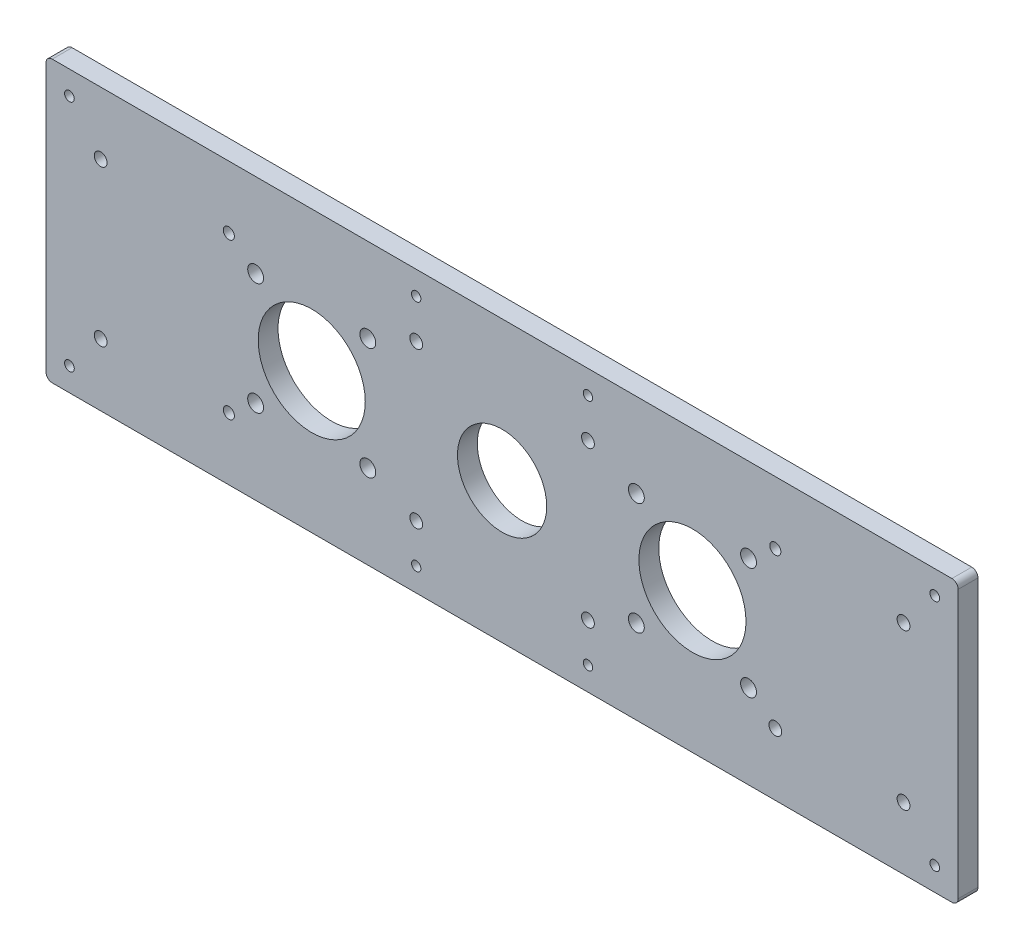
SolidWorks part; units mm, degrees
ref_plane "Front Plane" through (0, 0, 0) normal (0, 0, 1) x (1, 0, 0)
ref_plane "Top Plane" through (0, 0, 0) normal (0, 1, 0) x (1, 0, 0)
ref_plane "Right Plane" through (0, 0, 0) normal (1, 0, 0) x (0, 0, -1)
sketch "Sketch1" plane through (0, 0, 0) normal (0, 0, 1) x (1, 0, 0)
  line L1 (0, 0) -> (292.1, 0)
  line L2 (0, 0) -> (0, 89.8)
  line L3 (0, 89.8) -> (292.1, 89.8)
  line L4 (292.1, 0) -> (292.1, 89.8)
  circle A3 centre (146.05, 44.9) radius 14.2875
  point P7 (146.05, 44.9)
  circle B0 centre (103.0516, 62.8594) radius 2.54
  circle B1 centre (103.0494, 26.9384) radius 2.54
  circle B2 centre (67.1284, 26.9406) radius 2.54
  circle B3 centre (67.1306, 62.8616) radius 2.54
  circle B4 centre (85.09, 44.9) radius 17.145
  circle B5 centre (189.0506, 62.8616) radius 2.54
  circle B6 centre (224.9716, 62.8594) radius 2.54
  circle B7 centre (224.9694, 26.9384) radius 2.54
  circle B8 centre (189.0484, 26.9406) radius 2.54
  circle B9 centre (207.01, 44.9) radius 17.145
  dimension "D3" = 60.96
  dimension "D4" = 60.96
  dimension "D5" = 146.05
  dimension "D6" = 28.575
  dimension "D1" = 89.8
  dimension "D2" = 292.1
sketch_block_instance "Block1-1"
sketch_block "Block1" parameters "D1"=5.08, "D2"=34.29
sketch_block_instance "Block2-1"
sketch_block "Block2" parameters "D1"=5.08, "D2"=34.29
extrude "Boss-Extrude1" add sketch "Sketch1" along normal blind 6.35
sketch "Sketch2" plane through (0, 0, 6.35) normal (0, 0, 1) x (1, 0, 0)
  line L0 (292.1, 89.8) -> (0, 89.8) construction
  line L1 (108.55, 0) -> (183.55, 0)
  line L2 (108.55, 0) -> (108.55, 89.8)
  line L3 (108.55, 89.8) -> (183.55, 89.8)
  line L4 (183.55, 0) -> (183.55, 89.8)
  line L5 (108.55, 0) -> (183.55, 89.8) construction
  line L6 (108.55, 89.8) -> (183.55, 0) construction
  line L7 (108.55, 44.9) -> (146.05, 44.9) construction
  line L8 (108.55, 89.8) -> (-29.3949, 89.8)
  line L9 (108.55, 89.8) -> (108.55, -10.172)
  line L10 (108.55, -10.172) -> (-29.3949, -10.172)
  line L11 (-29.3949, 89.8) -> (-29.3949, -10.172)
  line L12 (183.55, 89.8) -> (343.3103, 89.8)
  line L13 (183.55, 89.8) -> (183.55, -29.3261)
  line L14 (183.55, -29.3261) -> (343.3103, -29.3261)
  line L15 (343.3103, 89.8) -> (343.3103, -29.3261)
  line L16 (146.05, 44.9) -> (146.05, 89.8) construction
  circle A0 centre (118.55, 20) radius 2.05
  circle A1 centre (118.55, 69.8) radius 2.05
  circle A2 centre (173.55, 20) radius 2.05
  circle A3 centre (173.55, 69.8) radius 2.05
  point P0 (146.05, 44.9)
  dimension "D2" = 4.1
  dimension "D3" = 20
  dimension "D1" = 75
  dimension "D4" = 10
extrude "Cut-Extrude1" cut sketch "Sketch2" against normal blind 10 contours A0 | A1 | A3 | A2
sketch "Sketch3" plane through (0, 0, 6.35) normal (0, 0, 1) x (1, 0, 0)
  line L0 (0, 0) -> (292.1, 0) construction
  line L1 (292.1, 0) -> (292.1, 89.8) construction
  line L2 (146.05, 0) -> (146.05, 11.9893) construction
  line L3 (292.1, 44.9) -> (277.1, 44.9) construction
  line L4 (173.55, 20) -> (173.55, 7.5)
  line L5 (173.55, 69.8) -> (173.55, 82.3)
  line L6 (118.55, 20) -> (118.55, 7.5)
  line L7 (118.55, 69.8) -> (118.55, 82.3)
  circle A0 centre (284.6, 7.5) radius 1.55
  circle A1 centre (7.5, 7.5) radius 1.55
  circle A2 centre (7.5, 82.3) radius 1.55
  circle A3 centre (284.6, 82.3) radius 1.55
  circle A4 centre (274.6, 20) radius 2.05
  circle A5 centre (17.5, 20) radius 2.05
  circle A6 centre (17.5, 69.8) radius 2.05
  circle A7 centre (274.6, 69.8) radius 2.05
  circle A8 centre (173.55, 20) radius 2.05 construction
  circle A9 centre (173.55, 7.5) radius 1.5
  circle A10 centre (173.55, 82.3) radius 1.5
  circle A11 centre (118.55, 82.3) radius 1.5
  circle A12 centre (118.55, 7.5) radius 1.5
  dimension "D1" = 3.1
  dimension "D4" = 4.1
  dimension "D7" = 3
  dimension "D8" = 3
  dimension "D9" = 3
  dimension "D10" = 3
  dimension "D2" = 7.5
  dimension "D3" = 7.5
  dimension "D5" = 10
  dimension "D6" = 0
extrude "Cut-Extrude2" cut sketch "Sketch3" against normal blind 10 contours A4 | A0 | A7 | A3 | A6 | A2 | A1 | A5 | A9 | A12 | A10 | A11
fillet "Fillet1" radius 2 4 edges at (0, 0, 3.175) (0, 89.8, 3.175) (292.1, 89.8, 3.175) (292.1, 0, 3.175)
sketch "Sketch4" plane through (0, 0, 6.35) normal (0, 0, 1) x (1, 0, 0)
  line L1 (233.55, 69.8) -> (58.55, 69.8)
  line L2 (233.55, 69.8) -> (233.55, 20)
  line L3 (233.55, 20) -> (58.55, 20)
  line L4 (58.55, 69.8) -> (58.55, 20)
  line L5 (233.55, 69.8) -> (58.55, 20) construction
  line L6 (233.55, 20) -> (58.55, 69.8) construction
  circle A0 centre (233.55, 20) radius 2.05
  circle A1 centre (233.55, 69.8) radius 1.778
  circle A2 centre (58.55, 69.8) radius 1.778
  circle A3 centre (58.55, 20) radius 1.778
  point P0 (146.05, 44.9)
  dimension "D2" = 4.1
  dimension "D3" = 3.556
  dimension "D4" = 3.556
  dimension "D5" = 3.556
  dimension "D1" = 175
extrude "Cut-Extrude4" cut sketch "Sketch4" against normal through all contours A0 | A1 | A2 | A3
